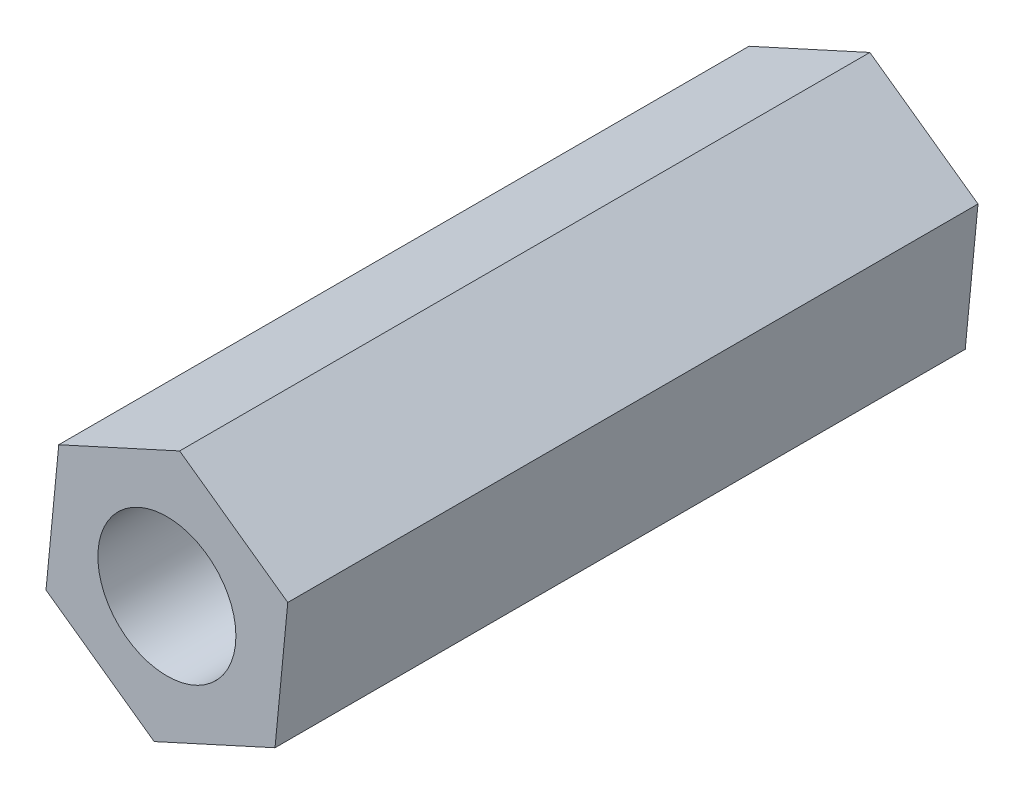
SolidWorks part; units mm, degrees
material "Mosiądz"
ref_plane "Płaszczyzna przednia" through (0, 0, 0) normal (0, 0, 1) x (1, 0, 0)
ref_plane "Płaszczyzna górna" through (0, 0, 0) normal (0, 1, 0) x (1, 0, 0)
ref_plane "Płaszczyzna prawa" through (0, 0, 0) normal (1, 0, 0) x (0, 0, -1)
sketch "Szkic1" plane through (0, 0, 0) normal (0, 0, 1) x (1, 0, 0)
  line L1 (2.627, 1.1967) -> (0.2771, 2.8734)
  line L2 (0.2771, 2.8734) -> (-2.3499, 1.6767)
  line L3 (-2.3499, 1.6767) -> (-2.627, -1.1967)
  line L4 (-2.627, -1.1967) -> (-0.2771, -2.8734)
  line L5 (-0.2771, -2.8734) -> (2.3499, -1.6767)
  line L6 (2.3499, -1.6767) -> (2.627, 1.1967)
  circle A0 centre (0, 0) radius 2.5 construction
  circle A1 centre (0, 0) radius 1.5
  dimension "D2" = 3
  dimension "D1" = 5
extrude "Dodanie-wyciągnięcie1" add sketch "Szkic1" along normal blind 15
